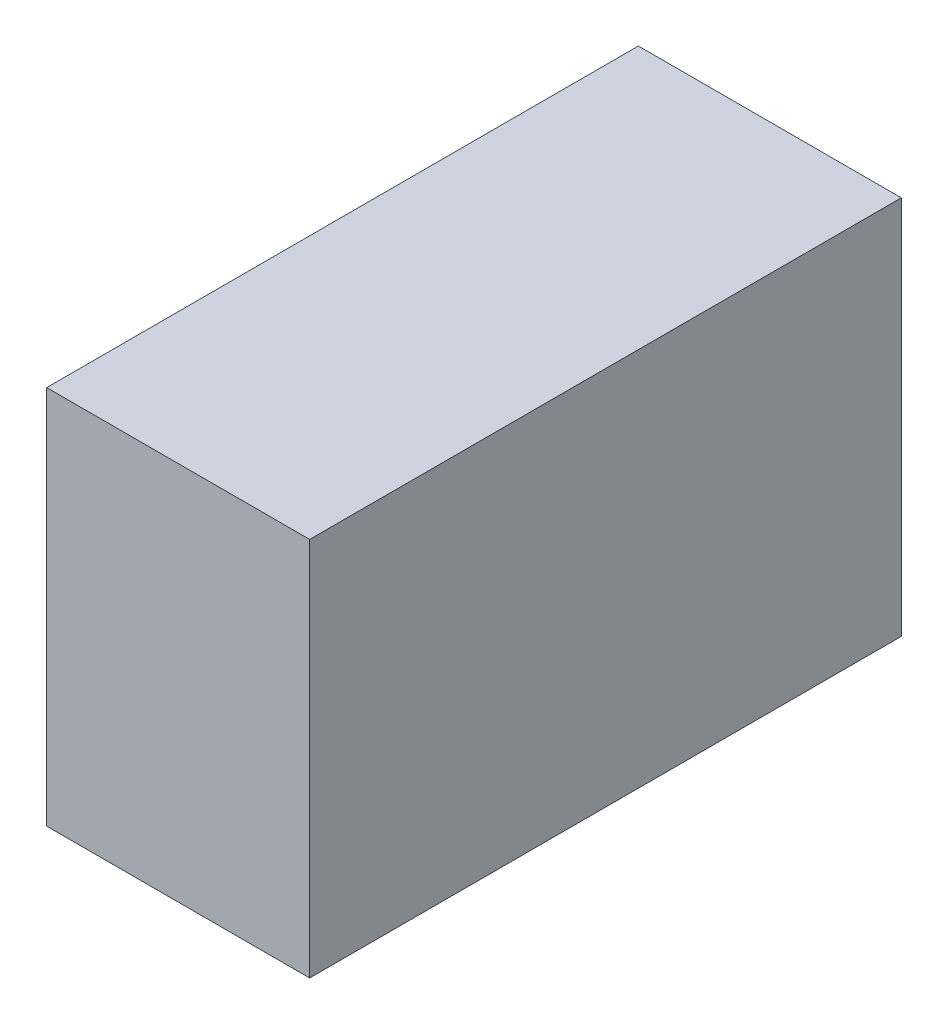
SolidWorks part; units mm, degrees
ref_plane "Front Plane" through (0, 0, 0) normal (0, 0, 1) x (1, 0, 0)
ref_plane "Top Plane" through (0, 0, 0) normal (0, 1, 0) x (1, 0, 0)
ref_plane "Right Plane" through (0, 0, 0) normal (1, 0, 0) x (0, 0, -1)
sketch "Sketch1" plane through (0, 0, 0) normal (0, 0, 1) x (1, 0, 0)
  line L1 (0, 0) -> (25.4, 0)
  line L2 (0, 0) -> (0, 36.6878)
  line L3 (0, 36.6878) -> (25.4, 36.6878)
  line L4 (25.4, 0) -> (25.4, 36.6878)
  dimension "D1" = 25.4
  dimension "D2" = 36.6878
extrude "Boss-Extrude1" add sketch "Sketch1" along normal blind 57.15
